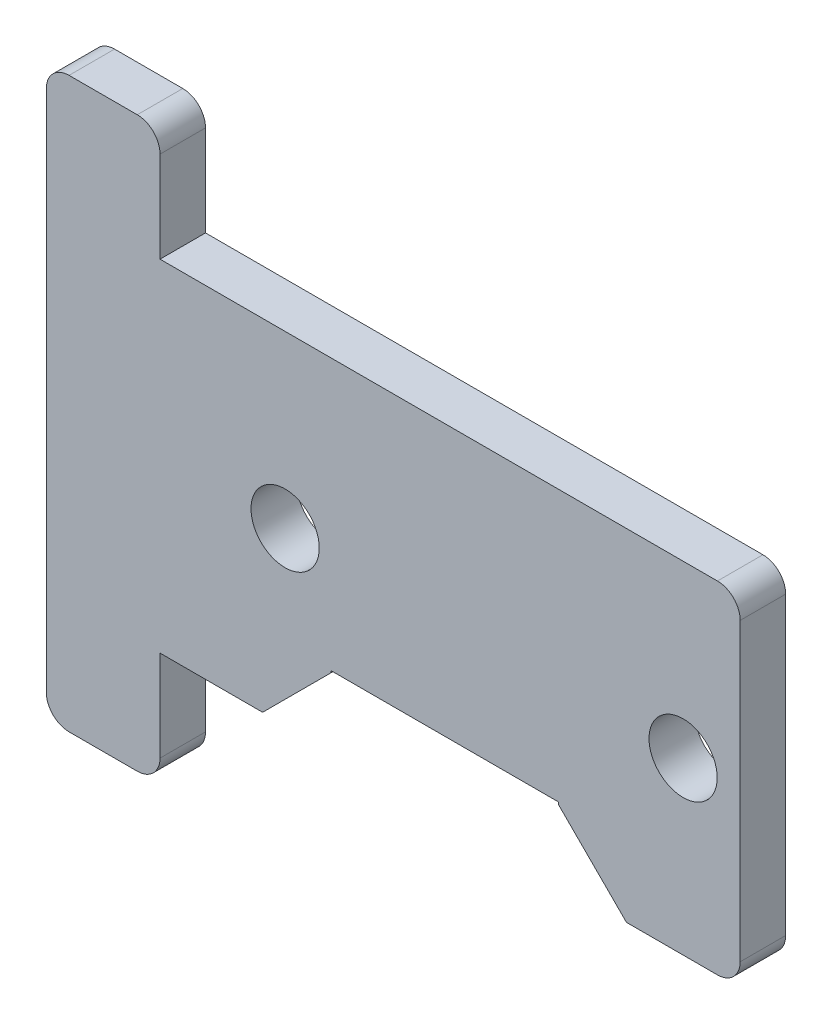
SolidWorks part; units mm, degrees
ref_plane "Front Plane" through (0, 0, 0) normal (0, 0, 1) x (1, 0, 0)
ref_plane "Top Plane" through (0, 0, 0) normal (0, 1, 0) x (1, 0, 0)
ref_plane "Right Plane" through (0, 0, 0) normal (1, 0, 0) x (0, 0, -1)
sketch "Sketch1" plane through (0, 0, 0) normal (0, 0, 1) x (1, 0, 0)
  line L0 (-10.6463, -7.6967) -> (-10.6463, -11.6967)
  line L1 (13.8637, -7.6967) -> (9.8637, -7.6967)
  line L2 (14.8637, -6.6967) -> (14.8637, 6.3033)
  line L3 (13.8637, 7.3033) -> (-10.6463, 7.3033)
  line L4 (-11.6463, -12.6967) -> (-14.6463, -12.6967)
  line L5 (-15.6463, -11.6967) -> (-15.6463, 11.3033)
  line L6 (-14.6463, 12.3033) -> (-11.6463, 12.3033)
  line L7 (-10.6463, 11.3033) -> (-10.6463, 7.3033)
  line L8 (-7.6463, 7.3033) -> (-7.6463, -7.6967) construction
  line L9 (14.8637, -0.1967) -> (-15.6463, -0.1967) construction
  line L10 (-3.1363, -4.6054) -> (-3.1363, -4.6967)
  line L11 (6.8637, -4.6054) -> (-3.1363, -4.6054)
  line L12 (6.8637, -4.6054) -> (6.8637, -4.6967)
  line L13 (-6.1363, -7.6967) -> (-10.6463, -7.6967)
  line L14 (6.8637, -4.6967) -> (9.8637, -7.6967)
  line L15 (-3.1363, -4.6967) -> (-6.1363, -7.6967)
  arc A0 (-15.6463, 11.3033) -> (-14.6463, 12.3033) centre (-14.6463, 11.3033) cw
  arc A1 (-14.6463, -12.6967) -> (-15.6463, -11.6967) centre (-14.6463, -11.6967) cw
  arc A2 (-10.6463, -11.6967) -> (-11.6463, -12.6967) centre (-11.6463, -11.6967) cw
  arc A3 (-11.6463, 12.3033) -> (-10.6463, 11.3033) centre (-11.6463, 11.3033) cw
  circle A4 centre (12.3537, -0.1967) radius 1.5
  circle A5 centre (-5.1463, -0.1967) radius 1.5
  arc A6 (13.8637, -7.6967) -> (14.8637, -6.6967) centre (13.8637, -6.6967) ccw
  arc A7 (14.8637, 6.3033) -> (13.8637, 7.3033) centre (13.8637, 6.3033) ccw
  point P22 (14.8637, -7.6967)
  point P25 (14.8637, 7.3033)
  point P32 (-3.1363, -7.6967)
  point P34 (6.8637, -7.6967)
  dimension "D3" = 1
  dimension "D5" = 3
  dimension "D6" = 3
  dimension "D9" = 1
  dimension "D1" = 5
  dimension "D2" = 15
  dimension "D4" = 3
  dimension "D7" = 2.51
  dimension "D8" = 17.5
  dimension "D10" = 2.5
  dimension "D11" = 10
  dimension "D12" = 8
extrude "Boss-Extrude1" add sketch "Sketch1" along normal blind 2
